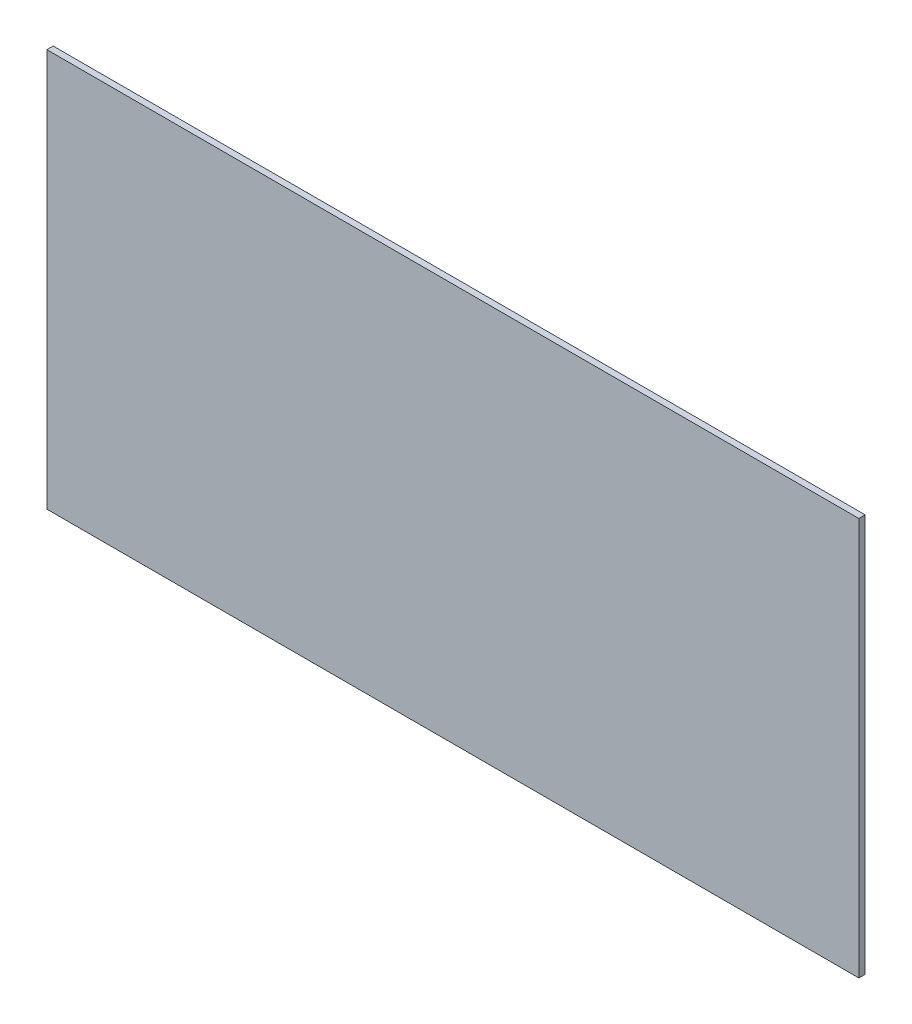
SolidWorks part; units mm, degrees
material "Acrylic (Medium-high impact)"
ref_plane "Front Plane" through (0, 0, 0) normal (0, 0, 1) x (1, 0, 0)
ref_plane "Top Plane" through (0, 0, 0) normal (0, 1, 0) x (1, 0, 0)
ref_plane "Right Plane" through (0, 0, 0) normal (1, 0, 0) x (0, 0, -1)
sketch "Sketch1" plane through (0, 0, 0) normal (0, 0, 1) x (1, 0, 0)
  line L1 (-289.5, -141.875) -> (289.5, -141.875)
  line L2 (-289.5, -141.875) -> (-289.5, 141.875)
  line L3 (-289.5, 141.875) -> (289.5, 141.875)
  line L4 (289.5, -141.875) -> (289.5, 141.875)
  line L5 (-289.5, -141.875) -> (289.5, 141.875) construction
  line L6 (-289.5, 141.875) -> (289.5, -141.875) construction
  point P0 (0, 0)
  dimension "D1" = 579
  dimension "D2" = 283.75
extrude "Boss-Extrude1" add sketch "Sketch1" along normal mid plane 4.4958
